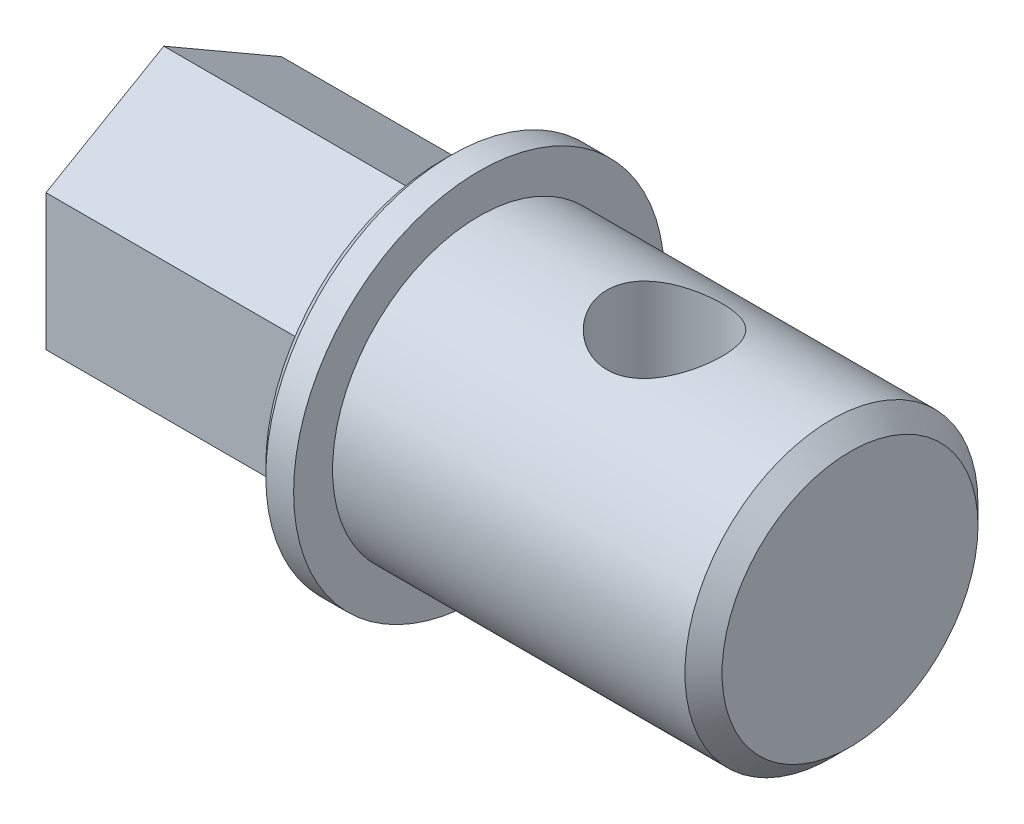
SolidWorks part; units mm, degrees
ref_plane "前视基准面" through (0, 0, 0) normal (0, 0, 1) x (1, 0, 0)
ref_plane "上视基准面" through (0, 0, 0) normal (0, 1, 0) x (1, 0, 0)
ref_plane "右视基准面" through (0, 0, 0) normal (1, 0, 0) x (0, 0, -1)
sketch "草图1" plane through (0, 0, 0) normal (1, 0, 0) x (0, 0, -1)
  circle A0 centre (0, 0) radius 7.9
extrude "凸台-拉伸1" add sketch "草图1" along normal blind 20
sketch "草图3" plane through (0, 0, 0) normal (-1, 0, 0) x (0, 0, 1)
  circle A0 centre (0, 0) radius 10
extrude "凸台-拉伸2" add sketch "草图3" along normal blind 2
sketch "草图4" plane through (-2, 0, 0) normal (-1, 0, 0) x (0, 0, 1)
  line L0 (0, 0) -> (0, 5) construction
  line L1 (6.35, 3.6662) -> (0, 7.3323)
  line L2 (0, 7.3323) -> (-6.35, 3.6662)
  line L3 (-6.35, 3.6662) -> (-6.35, -3.6662)
  line L4 (-6.35, -3.6662) -> (0, -7.3323)
  line L5 (0, -7.3323) -> (6.35, -3.6662)
  line L6 (6.35, -3.6662) -> (6.35, 3.6662)
  circle A0 centre (0, 0) radius 6.35 construction
  dimension "D1" = 12.7
  dimension "D2" = 60
extrude "凸台-拉伸3" add sketch "草图4" along normal blind 15
sketch "草图5" plane through (0, 0, 0) normal (0, 1, 0) x (1, 0, 0)
  line L0 (20, 0) -> (10, 0) construction
  line L1 (20, -7.9) -> (20, 7.9) construction
  circle A0 centre (10, 0) radius 3.1
extrude "切除-拉伸1" cut sketch "草图5" against normal mid plane 20
chamfer "倒角1" distance 0.5 angle 45 1 edges at (-2, 0, 10)
sketch "草图6" plane through (-17, 0, 0) normal (-1, 0, 0) x (0, 0, 1)
  circle A0 centre (0, 0) radius 2.6
  dimension "D1" = 5.2
extrude "切除-拉伸2" cut sketch "草图6" against normal blind 15
chamfer "倒角2" distance 1 angle 45 1 edges at (20, 0, -7.9)
